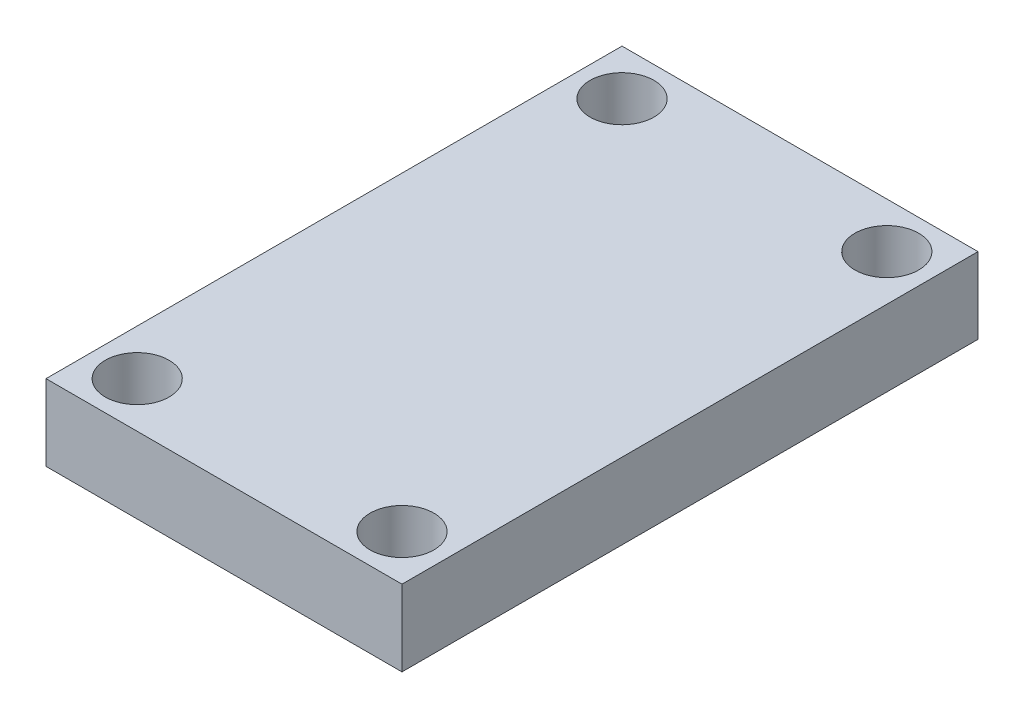
SolidWorks part; units mm, degrees
ref_plane "Front Plane" through (0, 0, 0) normal (0, 0, 1) x (1, 0, 0)
ref_plane "Top Plane" through (0, 0, 0) normal (0, 1, 0) x (1, 0, 0)
ref_plane "Right Plane" through (0, 0, 0) normal (1, 0, 0) x (0, 0, -1)
sketch "Sketch1" plane through (0, 0, 0) normal (0, 1, 0) x (1, 0, 0)
  line L0 (9.6073, -24.9772) -> (9.6073, 30.9748) construction
  line L1 (13.4173, 19.3458) -> (-16.3304, 19.3458)
  line L2 (13.4173, 19.3458) -> (13.4173, -28.7872)
  line L3 (13.4173, -28.7872) -> (-16.3304, -28.7872)
  line L4 (-16.3304, 19.3458) -> (-16.3304, -28.7872)
  line L5 (-12.5204, 26.6769) -> (-12.5204, -67.8757) construction
  line L6 (22.599, -24.9772) -> (-54.7622, -24.9772) construction
  line L7 (37.2508, 15.5358) -> (-46.948, 15.5358) construction
  circle A8 centre (9.6073, 15.5358) radius 2.667
  circle A9 centre (9.6073, -24.9772) radius 2.667
  circle A10 centre (-12.5204, -24.9772) radius 2.667
  circle A11 centre (-12.5204, 15.5358) radius 2.667
  point P33 (0, 0)
  dimension "D6" = 3.81
  dimension "D16" = 5.334
  dimension "D11" = 5.334
  dimension "D12" = 5.334
  dimension "D2" = 3.81
  dimension "D3" = 40.513
  dimension "D4" = 22.1276
  dimension "D5" = 3.81
  dimension "D7" = 3.81
  dimension "D9" = 3.81
extrude "Boss-Extrude1" add sketch "Sketch1" along normal blind 6.35
